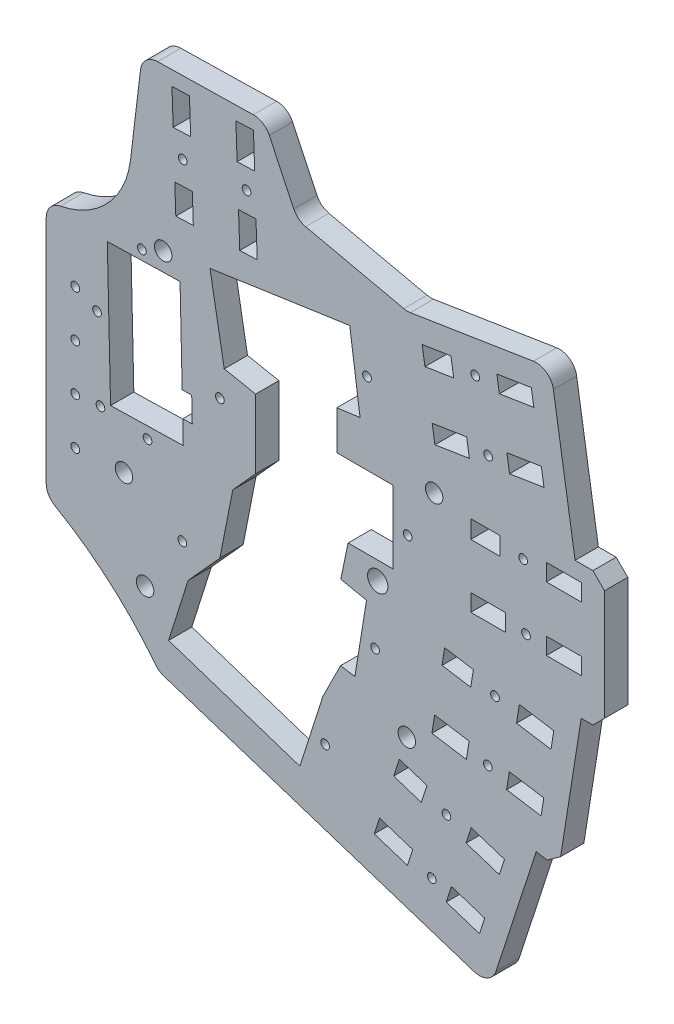
SolidWorks part; units mm, degrees
material "PMMA"
ref_plane "Front Plane" through (0, 0, 0) normal (0, 0, 1) x (1, 0, 0)
ref_plane "Top Plane" through (0, 0, 0) normal (0, 1, 0) x (1, 0, 0)
ref_plane "Right Plane" through (0, 0, 0) normal (1, 0, 0) x (0, 0, -1)
sketch "Sketch1" plane through (0, 0, 0) normal (0, 0, 1) x (1, 0, 0)
  line L16 (-82.5, 0) -> (-82.5, -22)
  line L17 (-82.5, 22) -> (-82.5, 0)
  line L18 (-65.9673, 52.0788) -> (-68.0005, 35.2008)
  line L19 (-60.9673, 52.1775) -> (-65.9673, 52.0788)
  line L20 (-44.9673, 52.4933) -> (-60.9673, 52.1775)
  line L21 (-39.3127, 40.6026) -> (-44.9673, 52.4933)
  line L22 (-20.4556, 36.3933) -> (-39.3127, 40.6026)
  line L23 (4.2366, 40.3042) -> (-20.4556, 36.3933)
  line L24 (8.4399, 13.7653) -> (4.2366, 40.3042)
  line L25 (13.5, 13.7653) -> (8.4399, 13.7653)
  line L26 (13.5, -9.2347) -> (13.5, 13.7653)
  line L27 (9.4917, -9.2347) -> (13.5, -9.2347)
  line L28 (5.6355, -33.5819) -> (9.4917, -9.2347)
  line L29 (1.75, -32.9665) -> (5.6355, -33.5819)
  line L30 (-6.0868, -57.0858) -> (1.75, -32.9665)
  line L31 (-63.1502, -38.5448) -> (-6.0868, -57.0858)
  line L32 (-82.5, 0) -> (-82.5, -22)
  line L33 (-82.5, 22) -> (-82.5, 0)
  line L34 (-65.9673, 52.0788) -> (-68.0005, 35.2008)
  line L35 (-60.9673, 52.1775) -> (-65.9673, 52.0788)
  line L36 (-44.9673, 52.4933) -> (-60.9673, 52.1775)
  line L37 (-39.3127, 40.6026) -> (-44.9673, 52.4933)
  line L38 (-20.4556, 36.3933) -> (-39.3127, 40.6026)
  line L39 (4.2366, 40.3042) -> (-20.4556, 36.3933)
  line L40 (8.4399, 13.7653) -> (4.2366, 40.3042)
  line L41 (13.5, 13.7653) -> (8.4399, 13.7653)
  line L42 (13.5, -9.2347) -> (13.5, 13.7653)
  line L43 (9.4917, -9.2347) -> (13.5, -9.2347)
  line L44 (5.6355, -33.5819) -> (9.4917, -9.2347)
  line L45 (1.75, -32.9665) -> (5.6355, -33.5819)
  line L46 (-6.0868, -57.0858) -> (1.75, -32.9665)
  line L47 (-63.1502, -38.5448) -> (-6.0868, -57.0858)
  arc A2 (-82.5, 22) -> (-68.0005, 35.2008) centre (-82.8929, 36.9949) ccw
  arc A3 (-63.1502, -38.5448) -> (-82.5, -22) centre (-110.9296, -74.8371) ccw
  arc A4 (-82.5, 22) -> (-68.0005, 35.2008) centre (-82.8929, 36.9949) ccw
  arc A5 (-63.1502, -38.5448) -> (-82.5, -22) centre (-110.9296, -74.8371) ccw
  dimension "D1" = 0
extrude "Boss-Extrude1" add sketch "Sketch1" against normal blind 4 contours L46 L45 L44 L43 L42 L41 L40 L39 L38 L37 L36 L35 L34 A4 L33 L32 A5 L47
fillet "Fillet2" radius 3 9 edges at (4.2366, 40.3042, -2) (-20.4556, 36.3933, -2) (-39.3127, 40.6026, -2) (-44.9673, 52.4933, -2) (-65.9673, 52.0788, -2) (-6.0868, -57.0858, -2) (-63.1502, -38.5448, -2) (-82.5, 22, -2) (-82.5, -22, -2)
chamfer "Chamfer1" distance 2 angle 45 3 edges at (5.6355, -33.5819, -2) (13.5, -9.2347, -2) (13.5, 13.7653, -2)
sketch "Sketch3" plane through (0, 0, -4) normal (0, 0, -1) x (-1, 0, 0)
  line L0 (12.8162, -45.4361) -> (7.1099, -47.2903)
  line L1 (12.8162, -45.4361) -> (13.7153, -48.2032)
  line L2 (7.1099, -47.2903) -> (8.009, -50.0573)
  line L3 (13.7153, -48.2032) -> (8.009, -50.0573)
  line L4 (25.18, -41.4189) -> (19.4736, -43.273)
  line L5 (25.18, -41.4189) -> (26.0931, -44.2291)
  line L6 (19.4736, -43.273) -> (20.3867, -46.0832)
  line L7 (26.0931, -44.2291) -> (20.3867, -46.0832)
  line L8 (21.7808, -30.9573) -> (17.0255, -32.5024)
  line L9 (21.7808, -30.9573) -> (22.7547, -33.9546)
  line L10 (17.0255, -32.5024) -> (17.9994, -35.4997)
  line L11 (22.7547, -33.9546) -> (17.9994, -35.4997)
  line L12 (9.417, -34.9745) -> (3.7107, -36.8286)
  line L13 (9.417, -34.9745) -> (10.3041, -37.7047)
  line L14 (3.7107, -36.8286) -> (4.5978, -39.5588)
  line L15 (10.3041, -37.7047) -> (4.5978, -39.5588)
  line L16 (15.7101, -21.3265) -> (9.784, -22.2651)
  line L17 (15.7101, -21.3265) -> (16.1814, -24.3021)
  line L18 (9.784, -22.2651) -> (10.2553, -25.2407)
  line L19 (16.1814, -24.3021) -> (10.2553, -25.2407)
  line L20 (2.8702, -23.3601) -> (-3.056, -24.2987)
  line L21 (2.8702, -23.3601) -> (3.3324, -26.2787)
  line L22 (-3.056, -24.2987) -> (-2.5937, -27.2173)
  line L23 (3.3324, -26.2787) -> (-2.5937, -27.2173)
  line L24 (13.9893, -10.4619) -> (9.0509, -11.2441)
  line L25 (13.9893, -10.4619) -> (14.4416, -13.3175)
  line L26 (9.0509, -11.2441) -> (9.5032, -14.0997)
  line L27 (14.4416, -13.3175) -> (9.5032, -14.0997)
  line L28 (1.1494, -12.4956) -> (-4.7767, -13.4342)
  line L29 (1.1494, -12.4956) -> (1.6282, -15.519)
  line L30 (-4.7767, -13.4342) -> (-4.2979, -16.4576)
  line L31 (1.6282, -15.519) -> (-4.2979, -16.4576)
  line L32 (9.5, 0) -> (3.5, 0)
  line L33 (9.5, 0) -> (9.5, -2.9458)
  line L34 (3.5, 0) -> (3.5, -2.9458)
  line L35 (9.5, -2.9458) -> (3.5, -2.9458)
  line L36 (-3.5, 0) -> (-9.5, 0)
  line L37 (-3.5, 0) -> (-3.5, -2.8751)
  line L38 (-9.5, 0) -> (-9.5, -2.8751)
  line L39 (-3.5, -2.8751) -> (-9.5, -2.8751)
  line L40 (9.5, 11) -> (4.5, 11)
  line L41 (9.5, 11) -> (9.5, 7.9089)
  line L42 (4.5, 11) -> (4.5, 7.9089)
  line L43 (9.5, 7.9089) -> (4.5, 7.9089)
  line L44 (-3.5, 11) -> (-9.5, 11)
  line L45 (-3.5, 11) -> (-3.5, 8.0831)
  line L46 (-9.5, 11) -> (-9.5, 8.0831)
  line L47 (-3.5, 8.0831) -> (-9.5, 8.0831)
  line L48 (16.1337, 21.8908) -> (10.2076, 22.8294)
  line L49 (16.1337, 21.8908) -> (15.6629, 18.9183)
  line L50 (10.2076, 22.8294) -> (9.7368, 19.8569)
  line L51 (15.6629, 18.9183) -> (9.7368, 19.8569)
  line L52 (3.2938, 23.9245) -> (-2.6324, 24.8631)
  line L53 (3.2938, 23.9245) -> (2.8325, 21.0124)
  line L54 (-2.6324, 24.8631) -> (-3.0936, 21.951)
  line L55 (2.8325, 21.0124) -> (-3.0936, 21.951)
  line L56 (17.8545, 32.7554) -> (12.9161, 33.5376)
  line L57 (17.8545, 32.7554) -> (17.3703, 29.6984)
  line L58 (12.9161, 33.5376) -> (12.4319, 30.4806)
  line L59 (17.3703, 29.6984) -> (12.4319, 30.4806)
  line L60 (5.0145, 34.7891) -> (-0.9116, 35.7277)
  line L61 (5.0145, 34.7891) -> (4.5813, 32.0537)
  line L62 (-0.9116, 35.7277) -> (-1.3448, 32.9923)
  line L63 (4.5813, 32.0537) -> (-1.3448, 32.9923)
extrude "Cut-Extrude1" cut sketch "Sketch3" against normal blind 10
sketch "Sketch4" plane through (0, 0, -4) normal (0, 0, -1) x (-1, 0, 0)
  line L0 (61.4619, -33.1128) -> (38.8752, -40.5573)
  line L1 (38.8752, -40.5573) -> (34.9412, -28.2056)
  line L3 (31.8905, -22.0823) -> (29.4225, -22.4809)
  line L4 (29.4225, -22.4809) -> (27.4252, -10.1139)
  line L5 (27.4252, -10.1139) -> (31.846, -9.1978)
  line L6 (31.846, -9.1978) -> (30.5966, -3.1687)
  line L7 (30.5966, -3.1687) -> (22.846, -3.1687)
  line L8 (22.846, -3.1687) -> (22.846, 9.3)
  line L9 (22.846, 9.3) -> (32.5343, 9.3)
  line L10 (32.5343, 9.3) -> (32.5343, 15.9983)
  line L11 (32.5343, 15.9983) -> (28.5335, 16.5375)
  line L12 (28.5335, 16.5375) -> (30.311, 29.36)
  line L13 (30.311, 29.36) -> (54.3357, 25.8419)
  line L14 (54.3357, 25.8419) -> (51.8868, 12.1157)
  line L15 (51.8868, 12.1157) -> (46.4956, 11.0567)
  line L16 (46.4956, 11.0567) -> (46.4956, -0.8192)
  line L17 (46.4956, -0.8192) -> (50.419, -5.16)
  line L18 (50.419, -5.16) -> (52.6347, -16.4399)
  line L19 (52.6347, -16.4399) -> (58.095, -22.4809)
  line L20 (58.095, -22.4809) -> (61.4619, -33.1128)
  line L21 (34.9412, -28.2056) -> (31.8905, -22.0823)
  point P0 (58.095, -22.0823)
  dimension "D1" = 2.5
extrude "Cut-Extrude2" cut sketch "Sketch4" against normal through all
sketch "Sketch5" plane through (0, 0, 0) normal (0, 0, 1) x (1, 0, 0)
  line L0 (-71.9944, 21.0289) -> (-71.4351, -3.1225)
  line L1 (-71.9944, 21.0289) -> (-59.4897, 21.3185)
  line L2 (-71.4351, -3.1225) -> (-58.9304, -2.8329)
  line L3 (-59.4897, 21.3185) -> (-58.9304, -2.8329)
extrude "Cut-Extrude3" cut sketch "Sketch5" against normal through all
sketch "Sketch6" plane through (0, 0, 0) normal (0, 0, 1) x (1, 0, 0)
  line L0 (-60.6706, 43.6827) -> (-60.88, 49.679)
  line L1 (-60.6706, 43.6827) -> (-57.6609, 43.7878)
  line L2 (-60.88, 49.679) -> (-57.8703, 49.7841)
  line L3 (-57.6609, 43.7878) -> (-57.8703, 49.7841)
  line L4 (-60.2169, 30.6906) -> (-60.3914, 35.6875)
  line L5 (-60.2169, 30.6906) -> (-57.2032, 30.7958)
  line L6 (-60.3914, 35.6875) -> (-57.3777, 35.7928)
  line L7 (-57.2032, 30.7958) -> (-57.3777, 35.7928)
  line L8 (-49.2236, 31.0745) -> (-49.433, 37.0708)
  line L9 (-49.2236, 31.0745) -> (-46.2234, 31.1792)
  line L10 (-49.433, 37.0708) -> (-46.4328, 37.1756)
  line L11 (-46.2234, 31.1792) -> (-46.4328, 37.1756)
  line L12 (-49.6773, 44.0665) -> (-49.8867, 50.0629)
  line L13 (-49.6773, 44.0665) -> (-46.6568, 44.172)
  line L14 (-49.8867, 50.0629) -> (-46.8662, 50.1684)
  line L15 (-46.6568, 44.172) -> (-46.8662, 50.1684)
extrude "Cut-Extrude4" cut sketch "Sketch6" against normal through all
sketch "Sketch7" plane through (0, 0, 0) normal (0, 0, 1) x (1, 0, 0)
  line L0 (-12.674, 32.0091) -> (-4.7979, 33.4214) construction
  line L1 (-12.4319, 30.4806) -> (-12.9161, 33.5376) construction
  line L2 (-5.0145, 34.7891) -> (-4.5813, 32.0537) construction
  line L3 (-9.9722, 21.3432) -> (-3.0632, 22.4684) construction
  line L4 (-9.7368, 19.8569) -> (-10.2076, 22.8294) construction
  line L5 (-3.2938, 23.9245) -> (-2.8325, 21.0124) construction
  line L6 (-4.5, 9.4544) -> (3.5, 9.5416) construction
  line L7 (-4.5, 7.9089) -> (-4.5, 11) construction
  line L8 (3.5, 11) -> (3.5, 8.0831) construction
  line L9 (-3.5, -1.4729) -> (3.5, -1.4375) construction
  line L10 (-3.5, -2.9458) -> (-3.5, 0) construction
  line L11 (3.5, 0) -> (3.5, -2.8751) construction
  line L12 (-9.277, -12.6719) -> (-1.3888, -14.0073) construction
  line L13 (-9.5032, -14.0997) -> (-9.0509, -11.2441) construction
  line L14 (-1.1494, -12.4956) -> (-1.6282, -15.519) construction
  line L15 (-10.0196, -23.7529) -> (-3.1013, -24.8194) construction
  line L16 (-10.2553, -25.2407) -> (-9.784, -22.2651) construction
  line L17 (-2.8702, -23.3601) -> (-3.3324, -26.2787) construction
  line L18 (-17.5124, -34.0011) -> (-9.8606, -36.3396) construction
  line L19 (-17.9994, -35.4997) -> (-17.0255, -32.5024) construction
  line L20 (-9.417, -34.9745) -> (-10.3041, -37.7047) construction
  line L21 (-19.9302, -44.6781) -> (-13.2658, -46.8197) construction
  line L22 (-20.3867, -46.0832) -> (-19.4736, -43.273) construction
  line L23 (-12.8162, -45.4361) -> (-13.7153, -48.2032) construction
  line L24 (-59.1658, 43.7352) -> (-58.8846, 35.7401) construction
  line L25 (-60.6706, 43.6827) -> (-57.6609, 43.7878) construction
  line L26 (-57.3777, 35.7928) -> (-60.3914, 35.6875) construction
  line L27 (-48.1671, 44.1193) -> (-47.9329, 37.1232) construction
  line L28 (-49.6773, 44.0665) -> (-46.6568, 44.172) construction
  line L29 (-46.4328, 37.1756) -> (-49.433, 37.0708) construction
  circle A0 centre (-59.0252, 39.7377) radius 0.75
  circle A1 centre (-48.05, 40.6212) radius 0.75
  circle A2 centre (-8.736, 32.7152) radius 0.75
  circle A3 centre (-6.5177, 21.9058) radius 0.75
  circle A4 centre (-0.5, 9.498) radius 0.75
  circle A5 centre (0, -1.4552) radius 0.75
  circle A6 centre (-5.3329, -13.3396) radius 0.75
  circle A7 centre (-6.5605, -24.2862) radius 0.75
  circle A8 centre (-13.6865, -35.1703) radius 0.75
  circle A9 centre (-16.2059, -45.8749) radius 0.75
  dimension "D1" = 1.5
extrude "Cut-Extrude5" cut sketch "Sketch7" against normal through all
sketch "Sketch8" plane through (0, 0, -4) normal (0, 0, -1) x (-1, 0, 0)
  circle A0 centre (65.076, -4.9507) radius 0.75
  circle A1 centre (66.0463, 22.8323) radius 0.75
  dimension "D1" = 1.5
  dimension "D2" = 1.5
extrude "Cut-Extrude6" cut sketch "Sketch8" against normal through all
sketch "Sketch9" plane through (0, 0, 0) normal (0, 0, 1) x (1, 0, 0)
  circle A0 centre (-27.3351, 23.2554) radius 0.75
  circle A1 centre (-54.7928, 18.9065) radius 0.75 construction
  circle A2 centre (-48.15, 3.1) radius 0.75 construction
  circle A3 centre (-20.35, 3.1) radius 0.75
  circle A4 centre (-53.3993, -12.2185) radius 0.75 construction
  circle A5 centre (-25.9416, -16.5673) radius 0.75
  circle A6 centre (-60.9803, -26.5271) radius 0.75 construction
  circle A7 centre (-34.541, -35.1178) radius 0.75
  dimension "D1" = 1.5
extrude "Cut-Extrude7" cut sketch "Sketch9" against normal through all
sketch "Sketch10" plane through (0, 0, 0) normal (0, 0, 1) x (1, 0, 0)
  line L0 (-82.5, -0.4597) -> (-77.5, -0.4597) construction
  line L1 (-82.5, 19.3175) -> (-82.5, -20.2369) construction
  line L2 (-77.5, -0.4597) -> (-77.5, 3.5403) construction
  line L3 (-77.5, 3.5403) -> (-77.5, 11.5403) construction
  circle A0 centre (-77.5, 3.5403) radius 0.75
  circle A1 centre (-77.5, 11.5403) radius 0.75
  circle A2 centre (-77.5, -4.4597) radius 0.75
  circle A3 centre (-77.5, -12.4597) radius 0.75
  dimension "D2" = 1.5
  dimension "D3" = 1.5
  dimension "D1" = 5
  dimension "D4" = 4
  dimension "D5" = 8
extrude "Cut-Extrude8" cut sketch "Sketch10" against normal through all
sketch "Sketch11" plane through (0, 0, -4) normal (0, 0, -1) x (-1, 0, 0)
  circle A0 centre (73.1762, -4.0914) radius 0.75
  circle A1 centre (73.7561, 9.7463) radius 0.75
  dimension "D1" = 1.5
  dimension "D2" = 1.5
extrude "Cut-Extrude9" cut sketch "Sketch11" against normal blind 5
sketch "Sketch12" plane through (0, 0, 0) normal (0, 0, 1) x (1, 0, 0)
  line L0 (-59.0218, 1.114) -> (-59.1206, 5.3779)
  line L1 (-59.0218, 1.114) -> (-57.3851, 1.1519)
  line L2 (-59.1206, 5.3779) -> (-57.4839, 5.4158)
  line L3 (-57.3851, 1.1519) -> (-57.4839, 5.4158)
  line L4 (-58.9304, -2.8329) -> (-59.4897, 21.3185) construction
  point P6 (-57.3851, 5.3779)
extrude "Cut-Extrude10" cut sketch "Sketch12" against normal blind 5
sketch "Sketch13" plane through (0, 0, 0) normal (0, 0, 1) x (1, 0, 0)
  circle A0 centre (-59.0905, -17.1588) radius 0.75
  circle A1 centre (-52.6347, 7.376) radius 0.75
  dimension "D1" = 1.5
  dimension "D2" = 1.5
extrude "Cut-Extrude11" cut sketch "Sketch13" against normal blind 5
sketch "Sketch14" plane through (0, 0, -4) normal (0, 0, -1) x (-1, 0, 0)
  line L0 (62.382, 24.4266) -> (69.1346, -11.952) construction
  line L1 (69.1346, -11.952) -> (25.5, -6.2934) construction
  line L2 (25.5, -6.2934) -> (62.382, 24.4266) construction
  line L3 (82.5, -0.4597) -> (0, 0) construction
  line L4 (82.5, 19.3175) -> (82.5, -20.2369) construction
  circle A0 centre (69.1346, -11.952) radius 1.5
  circle A1 centre (25.5, -6.2934) radius 1.75
  circle A2 centre (62.382, 24.4266) radius 1.5
  point P2 (59.5446, 23.6858)
  point P5 (61.382, 24.4322)
  point P9 (65.7249, -11.3819)
  point P10 (0, 0)
  dimension "D1" = 37
  dimension "D6" = 3.5
  dimension "D2" = 44
  dimension "D3" = 48
  dimension "D4" = 57
  dimension "D5" = 6.1512
extrude "Cut-Extrude12" cut sketch "Sketch14" against normal blind 5
sketch "Sketch15" plane through (0, 0, -4) normal (0, 0, -1) x (-1, 0, 0)
  line L0 (65.5, -27.0393) -> (20.5, -27.0393) construction
  line L1 (20.5, -27.0393) -> (15.8, 11.6764) construction
  line L2 (15.8, 11.6764) -> (65.5, -27.0393) construction
  line L3 (82.5, 19.3175) -> (82.5, -20.2369) construction
  line L4 (46.9039, 52.4551) -> (63.3599, 52.1302) construction
  circle A0 centre (65.5, -27.0393) radius 1.5
  circle A1 centre (20.5, -27.0393) radius 1.5
  circle A2 centre (15.8, 11.6764) radius 1.5
  point P6 (19.0094, -28.0352)
  point P11 (16.9717, 10.9115)
  point P12 (64.0094, -28.0352)
  dimension "D1" = 3
  dimension "D2" = 3
  dimension "D3" = 3
  dimension "D4" = 39
  dimension "D5" = 45
  dimension "D6" = 63
  dimension "D7" = 62
  dimension "D8" = 80
extrude "Cut-Extrude13" cut sketch "Sketch15" against normal through all
